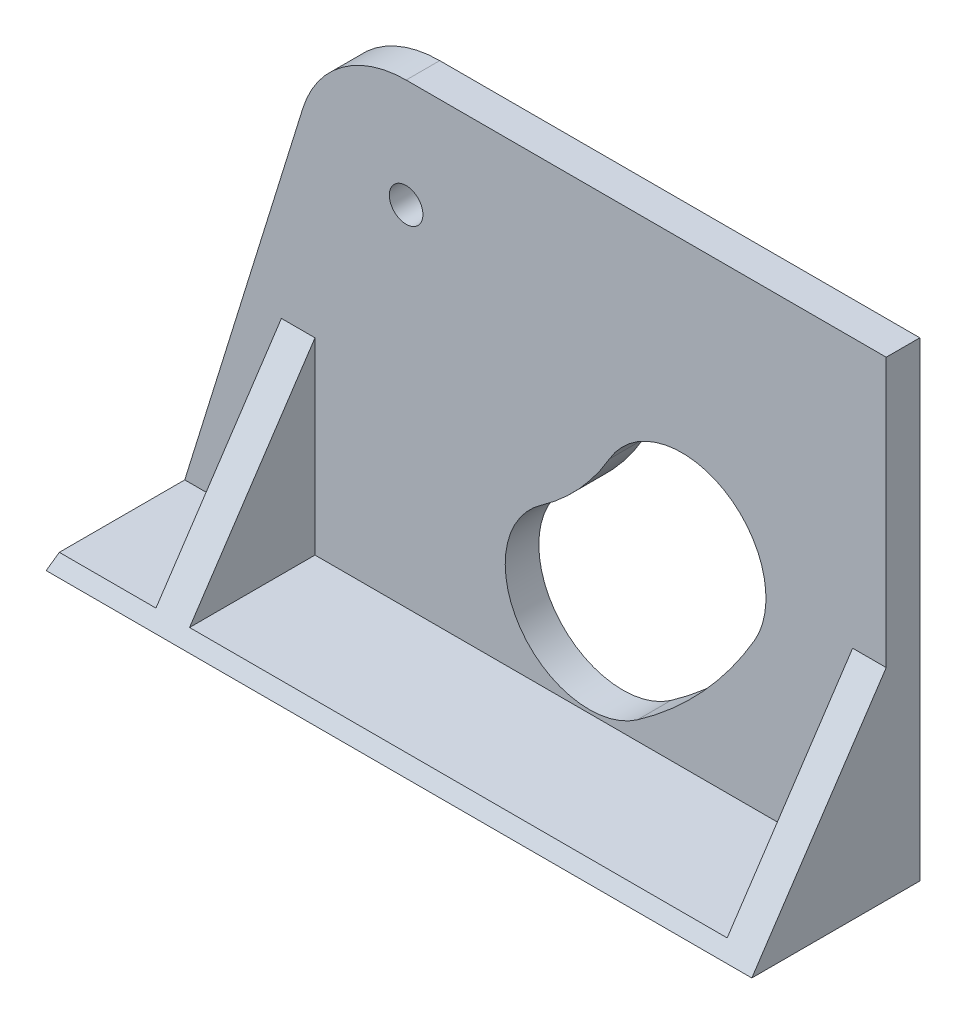
SolidWorks part; units mm, degrees
ref_plane "Front Plane" through (0, 0, 0) normal (0, 0, 1) x (1, 0, 0)
ref_plane "Top Plane" through (0, 0, 0) normal (0, 1, 0) x (1, 0, 0)
ref_plane "Right Plane" through (0, 0, 0) normal (1, 0, 0) x (0, 0, -1)
sketch "Sketch1" plane through (0, 0, 0) normal (0, 0, 1) x (1, 0, 0)
  line L1 (0, 0) -> (120, 0)
  line L2 (0, 0) -> (0, 100)
  line L3 (0, 100) -> (120, 100)
  line L4 (120, 0) -> (120, 100)
  dimension "D1" = 120
  dimension "D2" = 100
extrude "Boss-Extrude1" add sketch "Sketch1" along normal blind 5
sketch "Sketch2" plane through (0, 0, 5) normal (0, 0, 1) x (1, 0, 0)
  line L0 (0, 0) -> (120, 0) construction
  line L3 (82.976, 4.7606) -> (120, 30.6851) construction
  line L4 (120, 0) -> (120, 100) construction
  arc A0 (75.8063, 15) -> (89.605, 30) centre (48.5614, 53.9097) ccw construction
  arc A1 (82.976, 4.7606) -> (100.4059, 23.708) centre (48.5614, 53.9097) ccw
  arc A2 (68.6366, 25.2394) -> (78.804, 36.292) centre (48.5614, 53.9097) ccw
  arc A3 (68.6366, 25.2394) -> (82.976, 4.7606) centre (75.8063, 15) ccw
  arc A4 (100.4059, 23.708) -> (78.804, 36.292) centre (89.605, 30) ccw
  arc A5 (48.5614, 6.4097) -> (89.605, 30) centre (48.5614, 53.9097) ccw construction
  arc A6 (48.5614, -28.5903) -> (119.8476, 12.3823) centre (48.5614, 53.9097) ccw construction
  arc A7 (48.5614, 41.4097) -> (59.3623, 47.6177) centre (48.5614, 53.9097) ccw construction
  arc A8 (48.5614, 41.4097) -> (48.5614, -28.5903) centre (48.5614, 6.4097) ccw construction
  arc A9 (119.8476, 12.3823) -> (59.3623, 47.6177) centre (89.605, 30) ccw construction
  circle A10 centre (48.5614, 53.9097) radius 2.5
  point P3 (83.5196, 21.7512)
  point P17 (72.2314, 12.7274)
  point P27 (115, 5)
  dimension "D1" = 47.5
  dimension "D3" = 12.5
  dimension "D6" = 5
  dimension "D5" = 35
  dimension "D9" = 5
  dimension "D2" = 15
  dimension "D4" = 30
  dimension "D7" = 5
  dimension "D8" = 35
extrude "Cut-Extrude1" cut sketch "Sketch2" against normal through all
sketch "Sketch3" plane through (0, 0, 0) normal (0, 0, -1) x (-1, 0, 0)
  line L0 (0, 100) -> (0, 0) construction
  line L1 (-120, 0) -> (0, 0)
  line L2 (-120, 0) -> (-120, 2)
  line L3 (-120, 2) -> (0, 2)
  line L4 (0, 0) -> (0, 2)
  dimension "D1" = 2
extrude "Boss-Extrude2" add sketch "Sketch3" along normal blind 20
sketch "Sketch4" plane through (0, 0, 5) normal (0, 0, 1) x (1, 0, 0)
  line L0 (89.605, 30) -> (48.5614, 53.9097) construction
  line L1 (48.5614, 53.9097) -> (75.8063, 15) construction
  line L2 (92.6251, 35.1845) -> (51.5816, 59.0942) construction
  line L3 (52.6571, 56.7776) -> (79.902, 17.8679) construction
  line L4 (120, 0) -> (120, 100) construction
  line L5 (0, 0) -> (120, 0) construction
  arc A0 (65.8054, 38) -> (73, 46.617) centre (63.0497, 47.6128) ccw construction
  arc A1 (66.4943, 35.5968) -> (75.4876, 46.368) centre (63.0497, 47.6128) ccw
  arc A2 (65.1165, 40.4032) -> (70.5124, 46.8659) centre (63.0497, 47.6128) ccw
  arc A3 (65.1165, 40.4032) -> (66.4943, 35.5968) centre (65.8054, 38) ccw
  arc A4 (75.4876, 46.368) -> (70.5124, 46.8659) centre (73, 46.617) ccw
  point P13 (70.7259, 41.2037)
  dimension "D3" = 2.5
  dimension "D4" = 10
  dimension "D5" = 47
  dimension "D6" = 38
  dimension "D1" = 6
  dimension "D2" = 5
extrude "Cut-Extrude2" cut sketch "Sketch4" against normal through all
sketch "Sketch5" plane through (0, 0, 5) normal (0, 0, 1) x (1, 0, 0)
  line L0 (120, 70) -> (48.5614, 70)
  line L1 (120, 0) -> (120, 100) construction
  line L2 (33.1929, 58.6749) -> (15, 0)
  line L3 (0, 0) -> (120, 0) construction
  line L4 (15, 0) -> (0, 0)
  line L5 (0, 0) -> (0, 100)
  line L6 (0, 100) -> (120, 100)
  line L7 (120, 100) -> (120, 70)
  arc A0 (48.5614, 70) -> (33.1929, 58.6749) centre (48.5614, 53.9097) ccw
  circle A1 centre (48.5614, 53.9097) radius 2.5 construction
  dimension "D1" = 15
  dimension "D2" = 70
extrude "Cut-Extrude3" cut sketch "Sketch5" against normal through all
sketch "Sketch6" plane through (0, 0, 0) normal (0, 0, -1) x (-1, 0, 0)
  line L0 (-120, 2) -> (-120, 70) construction
  line L1 (-120, 30) -> (-115, 30)
  line L2 (-120, 30) -> (-120, 0)
  line L3 (-120, 0) -> (-115, 0)
  line L4 (-115, 30) -> (-115, 0)
  line L5 (-120, 0) -> (-15, 0) construction
  line L7 (-35, 0) -> (-30, 0)
  line L8 (-35, 0) -> (-35, 30)
  line L9 (-35, 30) -> (-30, 30)
  line L10 (-30, 0) -> (-30, 30)
  dimension "D1" = 5
  dimension "D2" = 30
  dimension "D3" = 5
  dimension "D4" = 30
  dimension "D5" = 80
extrude "Boss-Extrude3" add sketch "Sketch6" along normal through all
sketch "Sketch9" plane through (120, 0, 0) normal (1, 0, 0) x (0, 0, -1)
  line L0 (0, 30) -> (20, 0)
  line L1 (20, 30) -> (0, 30) construction
  line L2 (20, 0) -> (20, 30)
  line L3 (20, 30) -> (0, 30)
extrude "Cut-Extrude4" cut sketch "Sketch9" against normal through all
mirror "Mirror1" about plane through (0, 0, 5) normal (0, 0, -1) of "Cut-Extrude1", "Cut-Extrude3", "Boss-Extrude1", "Boss-Extrude2", "Boss-Extrude3", "Cut-Extrude4"
sketch "Sketch10" plane through (120, 0, 0) normal (1, 0, 0) x (0, 0, -1)
  line L0 (0, 70) -> (-10, 70) construction
  line L1 (-5, 70) -> (22.8846, 70)
  line L2 (-5, 70) -> (-5, 0)
  line L3 (-5, 0) -> (22.8846, 0)
  line L4 (22.8846, 70) -> (22.8846, 0)
  line L5 (-30, 0) -> (20, 0) construction
  dimension "D1" = 27.8846
extrude "Cut-Extrude5" cut sketch "Sketch10" against normal through all
